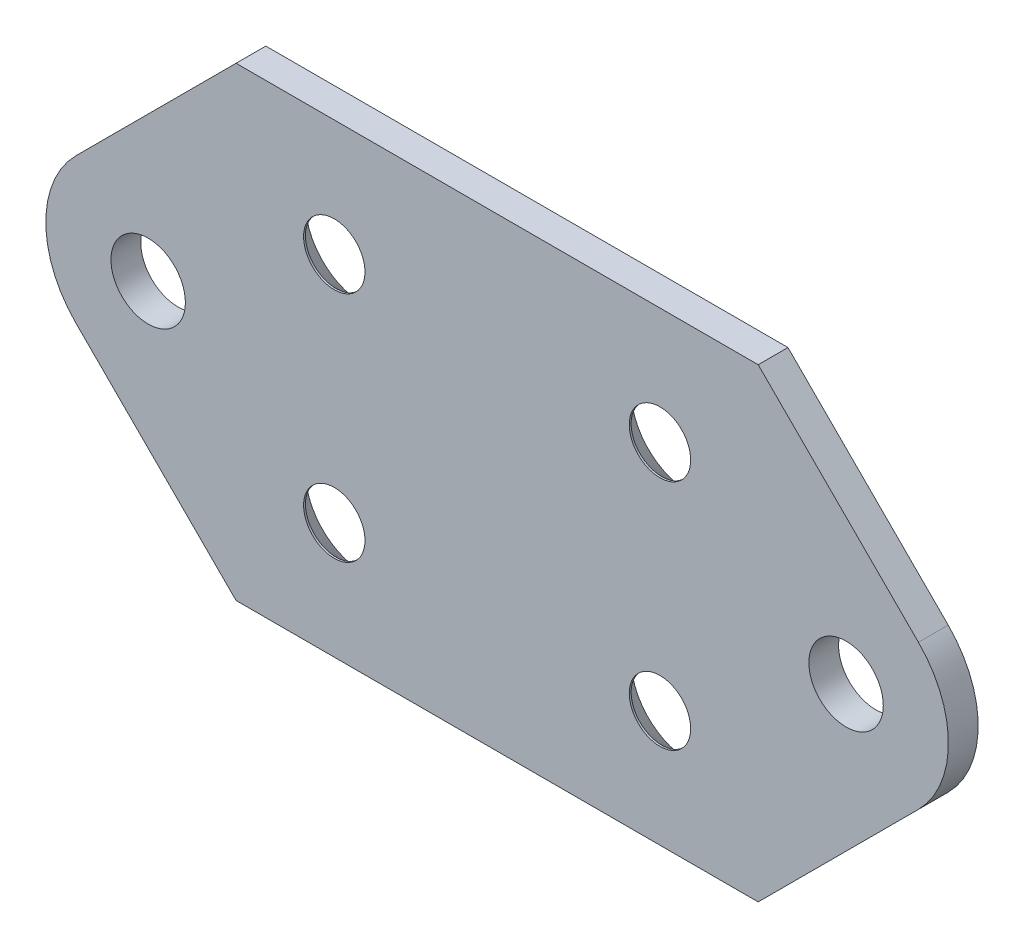
SolidWorks part; units mm, degrees
material "Plain Carbon Steel"
ref_plane "Front Plane" through (0, 0, 0) normal (0, 0, 1) x (1, 0, 0)
ref_plane "Top Plane" through (0, 0, 0) normal (0, 1, 0) x (1, 0, 0)
ref_plane "Right Plane" through (0, 0, 0) normal (1, 0, 0) x (0, 0, -1)
sketch "Sketch1" plane through (0, 0, 0) normal (0, 0, 1) x (1, 0, 0)
  line L0 (9.4437, 25) -> (65.5563, 25)
  line L1 (9.4437, -25) -> (65.5563, -25)
  line L6 (9.4437, 25) -> (-7.7782, 7.7782)
  line L7 (9.4437, -25) -> (-7.7782, -7.7782)
  line L8 (0, 0) -> (75, 0) construction
  line L9 (37.5, 0) -> (37.5, 25) construction
  line L10 (65.5563, -25) -> (82.7782, -7.7782)
  line L11 (65.5563, 25) -> (82.7782, 7.7782)
  circle A0 centre (0, 0) radius 4
  circle A1 centre (75, 0) radius 4
  arc A4 (-7.7782, 7.7782) -> (-7.7782, -7.7782) centre (0, 0) ccw
  arc A5 (82.7782, 7.7782) -> (82.7782, -7.7782) centre (75, 0) cw
  point P20 (37.5, -25)
  dimension "D1" = 8
  dimension "D2" = 8
  dimension "D6" = 90
  dimension "D9" = 11
  dimension "D3" = 75
  dimension "D4" = 50
  dimension "D5" = 25
  dimension "D8" = 135
extrude "Boss-Extrude1" add sketch "Sketch1" along normal blind 3.2
hole_wizard "CSK for M6 Flat Head Machine Screw1" positions "Sketch12" profile "Sketch13" countersink size "M6" standard "ANSI Metric" end condition through all
sketch "Sketch12" plane through (0, 0, 0) normal (0, 0, 1) x (1, 0, 0)
  line L0 (0, 0) -> (75, 0) construction
  line L2 (37.5, 0) -> (37.5, 25) construction
  line L3 (65.5563, 25) -> (9.4437, 25) construction
  point P13 (20, 12.5)
  point P15 (55, 12.5)
  point P17 (55, -12.5)
  point P19 (20, -12.5)
  dimension "D1" = 17.5
  dimension "D2" = 17.5
  dimension "D3" = 12.5
  dimension "D4" = 12.5
  dimension "D5" = 12.5
  dimension "D6" = 12.5
  dimension "D7" = 17.5
  dimension "D8" = 17.5
sketch "Sketch13" plane through (20, -12.5, 0) normal (1, 0, 0) x (0, 1, 0)
  line L0 (0, 0) -> (0, 3.2)
  line L1 (0, 3.2) -> (3.3, 3.2)
  line L2 (3.3, 3.2) -> (3.3, 3)
  line L3 (3.3, 3) -> (6.3, 0)
  line L5 (6.3, 0) -> (0, 0)
  line L6 (-3.3, 3) -> (-6.3, 0) construction
  line L11 (0, -6.35) -> (0, 107.95) construction
  dimension "Thru Hole Dia." = 6.6
  dimension "Thru Hole Depth" = 3.2
  dimension "Near C'Sink Dia." = 12.6
  dimension "Near C'Sink Angle" = 90
